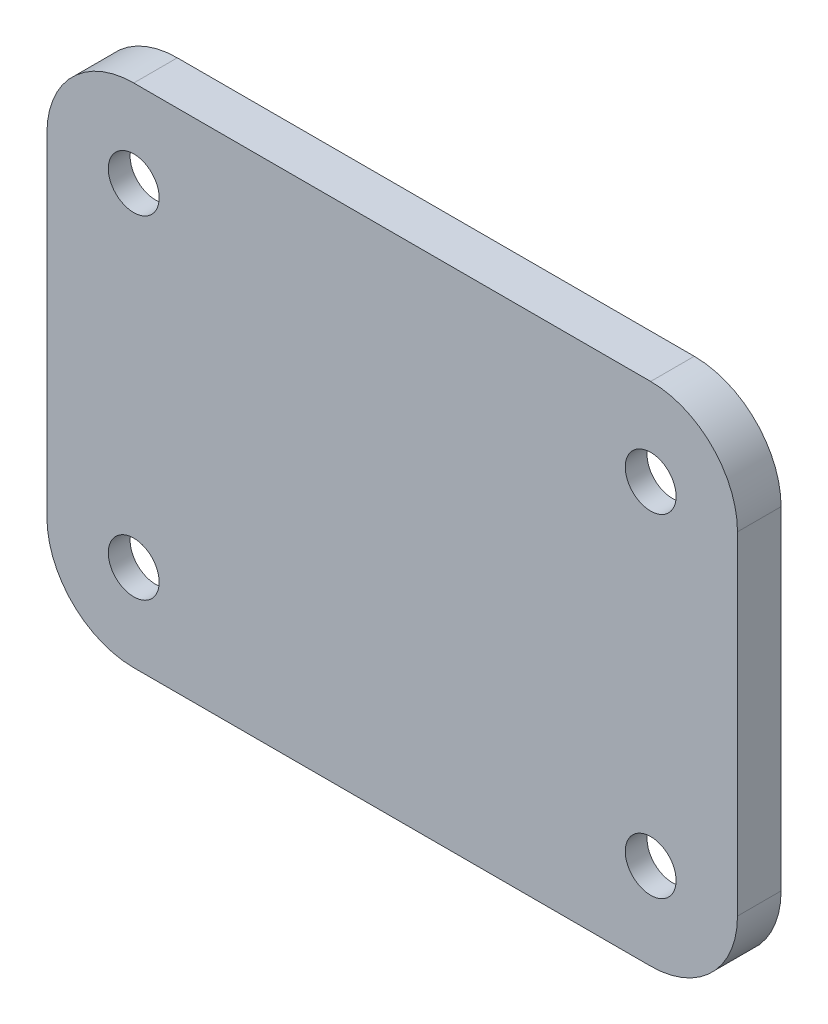
SolidWorks part; units mm, degrees
ref_plane "Front Plane" through (0, 0, 0) normal (0, 0, 1) x (1, 0, 0)
ref_plane "Top Plane" through (0, 0, 0) normal (0, 1, 0) x (1, 0, 0)
ref_plane "Right Plane" through (0, 0, 0) normal (1, 0, 0) x (0, 0, -1)
sketch "Sketch1" plane through (0, 0, 0) normal (0, 0, 1) x (1, 0, 0)
  line L4 (-17.7875, 11.45) -> (-17.7875, 17.425) construction
  line L5 (23.7625, -17.425) -> (-23.7625, -17.425)
  line L6 (23.7625, -17.425) -> (23.7625, 17.425)
  line L7 (23.7625, 17.425) -> (-23.7625, 17.425)
  line L8 (-22.275, 11.45) -> (-22.275, -11.45)
  line L9 (-18.1222, -15.925) -> (18.1222, -15.925)
  line L10 (22.275, -11.45) -> (22.275, 11.45)
  line L11 (18.1222, 15.925) -> (-18.1222, 15.925)
  line L12 (-22.275, 11.45) -> (-22.275, -11.45)
  line L13 (-18.1222, -15.925) -> (18.1222, -15.925)
  line L14 (22.275, -11.45) -> (22.275, 11.45)
  line L15 (18.1222, 15.925) -> (-18.1222, 15.925)
  line L16 (-23.7625, -17.425) -> (-23.7625, 17.425)
  line L17 (23.7625, -17.425) -> (-23.7625, 17.425) construction
  line L18 (23.7625, 17.425) -> (-23.7625, -17.425) construction
  line L19 (-17.7875, 11.45) -> (-23.7625, 11.45) construction
  circle A0 centre (-17.7875, 11.45) radius 1.4
  circle A1 centre (-17.7875, 11.45) radius 1.4 construction
  circle A2 centre (17.7875, 11.45) radius 1.4
  circle A3 centre (17.7875, 11.45) radius 1.4 construction
  circle A4 centre (17.7875, -11.45) radius 1.4
  circle A5 centre (17.7875, -11.45) radius 1.4 construction
  circle A6 centre (-17.7875, -11.45) radius 1.4
  circle A7 centre (-17.7875, -11.45) radius 1.4 construction
  circle A8 centre (-17.7875, 11.45) radius 5.975
  circle A9 centre (17.7875, 11.45) radius 5.975
  circle A10 centre (17.7875, -11.45) radius 5.975
  circle A11 centre (-17.7875, -11.45) radius 5.975
  circle A12 centre (-17.7875, 11.45) radius 1.75
  circle A13 centre (17.7875, 11.45) radius 1.75
  circle A14 centre (17.7875, -11.45) radius 1.75
  circle A15 centre (-17.7875, -11.45) radius 1.75
  arc A16 (22.275, 11.45) -> (18.1222, 15.925) centre (17.7875, 11.45) ccw
  arc A17 (22.275, 11.45) -> (18.1222, 15.925) centre (17.7875, 11.45) ccw
  arc A18 (-18.1222, 15.925) -> (-22.275, 11.45) centre (-17.7875, 11.45) ccw
  arc A19 (-18.1222, 15.925) -> (-22.275, 11.45) centre (-17.7875, 11.45) ccw
  arc A20 (-22.275, -11.45) -> (-18.1222, -15.925) centre (-17.7875, -11.45) ccw
  arc A21 (-22.275, -11.45) -> (-18.1222, -15.925) centre (-17.7875, -11.45) ccw
  arc A22 (18.1222, -15.925) -> (22.275, -11.45) centre (17.7875, -11.45) ccw
  arc A23 (18.1222, -15.925) -> (22.275, -11.45) centre (17.7875, -11.45) ccw
  point P24 (0, 0)
  dimension "D3" = 3.5
  dimension "D2" = 1.5
  dimension "D1" = 0.25
extrude "Boss-Extrude1" add sketch "Sketch1" along normal blind 1.5 contours L15 A19 L12 A8 A0 | A19 L15 A8 L12 | A11 L12 A8 L16 | A21 L12 A11 L13 | L12 A21 L13 A11 A6 | A11 L13 A10 L14 A9 L15 A8 L12 | A9 L7 A8 L15 | A17 L14 A9 L15 | L14 A17 L15 A9 A2 | L13 A23 L14 A10 A4 | A10 L6 A9 L14 | A23 L13 A10 L14 | A11 L5 A10 L13
sketch "Sketch2" plane through (0, 0, 0) normal (0, 0, -1) x (-1, 0, 0)
  line L0 (17.7875, 15.925) -> (-17.7875, 15.925)
  line L1 (-22.2625, 11.45) -> (-22.2625, -11.45)
  line L2 (-17.7875, -15.925) -> (17.7875, -15.925)
  line L3 (22.2625, -11.45) -> (22.2625, 11.45)
  line L4 (-17.7875, -17.425) -> (17.7875, -17.425)
  line L5 (-23.7625, 11.45) -> (-23.7625, -11.45)
  line L6 (17.7875, 17.425) -> (-17.7875, 17.425)
  line L7 (23.7625, -11.45) -> (23.7625, 11.45)
  line L8 (-17.7875, -17.425) -> (17.7875, -17.425)
  line L9 (-23.7625, 11.45) -> (-23.7625, -11.45)
  line L10 (17.7875, 17.425) -> (-17.7875, 17.425)
  line L11 (23.7625, -11.45) -> (23.7625, 11.45)
  arc A0 (22.2625, 11.45) -> (17.7875, 15.925) centre (17.7875, 11.45) ccw
  arc A1 (-17.7875, 15.925) -> (-22.2625, 11.45) centre (-17.7875, 11.45) ccw
  arc A2 (-22.2625, -11.45) -> (-17.7875, -15.925) centre (-17.7875, -11.45) ccw
  arc A3 (17.7875, -15.925) -> (22.2625, -11.45) centre (17.7875, -11.45) ccw
  arc A4 (-23.7625, -11.45) -> (-17.7875, -17.425) centre (-17.7875, -11.45) ccw
  arc A5 (-17.7875, 17.425) -> (-23.7625, 11.45) centre (-17.7875, 11.45) ccw
  arc A6 (23.7625, 11.45) -> (17.7875, 17.425) centre (17.7875, 11.45) ccw
  arc A7 (17.7875, -17.425) -> (23.7625, -11.45) centre (17.7875, -11.45) ccw
  arc A8 (-23.7625, -11.45) -> (-17.7875, -17.425) centre (-17.7875, -11.45) ccw
  arc A9 (-17.7875, 17.425) -> (-23.7625, 11.45) centre (-17.7875, 11.45) ccw
  arc A10 (23.7625, 11.45) -> (17.7875, 17.425) centre (17.7875, 11.45) ccw
  arc A11 (17.7875, -17.425) -> (23.7625, -11.45) centre (17.7875, -11.45) ccw
  dimension "D2" = 1.5
  dimension "D1" = 0
extrude "Boss-Extrude2" add sketch "Sketch2" along normal blind 1.5
sketch "Sketch3" plane through (0, 0, 0) normal (0, 0, -1) x (-1, 0, 0)
  line L0 (-22.2625, 11.45) -> (-22.2625, -11.45) construction
  line L1 (22.2625, -6.975) -> (-22.2625, -6.975)
  line L2 (22.2625, -6.975) -> (22.2625, 6.975)
  line L3 (22.2625, 6.975) -> (-22.2625, 6.975)
  line L4 (-22.2625, -6.975) -> (-22.2625, 6.975)
  line L5 (22.2625, -6.975) -> (-22.2625, 6.975) construction
  line L6 (22.2625, 6.975) -> (-22.2625, -6.975) construction
  line L7 (17.7875, 15.925) -> (-17.7875, 15.925) construction
  line L8 (-13.3125, -15.925) -> (13.3125, -15.925)
  line L9 (-13.3125, -15.925) -> (-13.3125, 15.925)
  line L10 (-13.3125, 15.925) -> (13.3125, 15.925)
  line L11 (13.3125, -15.925) -> (13.3125, 15.925)
  line L12 (-13.3125, -15.925) -> (13.3125, 15.925) construction
  line L13 (-13.3125, 15.925) -> (13.3125, -15.925) construction
  circle A0 centre (17.7875, 11.45) radius 4.475
  arc A1 (22.2625, 11.45) -> (17.7875, 15.925) centre (17.7875, 11.45) ccw construction
  circle A2 centre (-17.7875, 11.45) radius 4.475
  circle A3 centre (-17.7875, -11.45) radius 4.475
  circle A4 centre (17.7875, -11.45) radius 4.475
  circle A5 centre (17.7875, -11.45) radius 1.75 construction
  circle A6 centre (-17.7875, 11.45) radius 1.75 construction
  circle A7 centre (-17.7875, -11.45) radius 1.75 construction
  point P0 (0, 0)
  point P8 (0, 0)
  point P30 (17.7875, -11.45)
  line M3 (22.2625, -11.45) -> (22.2625, 11.45)
  line M5 (17.7875, 15.925) -> (-17.7875, 15.925)
  line M7 (-22.2625, 11.45) -> (-22.2625, -11.45)
  line M9 (-17.7875, -15.925) -> (17.7875, -15.925)
extrude "Cut-Extrude1" cut sketch "Sketch3" against normal blind 0.5 contours A2 L3 L9 | L1 L9 L3 M7 | L3 L11 L9 M5 | A0 L11 L3 | L11 L1 L3 M3 | A4 L1 L11 | L11 L1 L9 M9 | L1 L11 L3 L9
sketch "Sketch4" plane through (0, 0, 1.5) normal (0, 0, 1) x (1, 0, 0)
  circle A0 centre (-17.7875, 11.45) radius 3
  circle A1 centre (17.7875, 11.45) radius 3
  circle A2 centre (17.7875, -11.45) radius 3
  circle A3 centre (-17.7875, -11.45) radius 3
  circle A4 centre (-17.7875, 11.45) radius 1.75 construction
  circle A5 centre (17.7875, 11.45) radius 1.75 construction
  circle A6 centre (-17.7875, -11.45) radius 1.75 construction
  circle A7 centre (17.7875, -11.45) radius 1.75 construction
  dimension "D1" = 6
extrude "Cut-Extrude2" [suppressed] cut sketch "Sketch4" against normal blind 0.4
chamfer "Chamfer1" [suppressed] distance 1.2 angle 45
